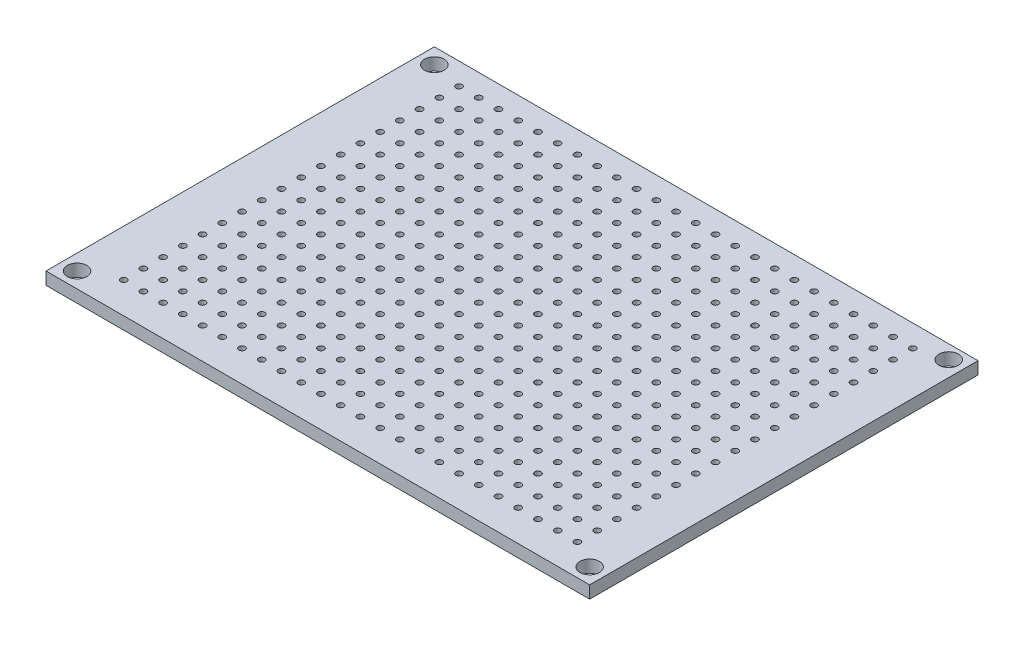
SolidWorks part; units mm, degrees
ref_plane "Front Plane" through (0, 0, 0) normal (0, 0, 1) x (1, 0, 0)
ref_plane "Top Plane" through (0, 0, 0) normal (0, 1, 0) x (1, 0, 0)
ref_plane "Right Plane" through (0, 0, 0) normal (1, 0, 0) x (0, 0, -1)
sketch "Sketch1" plane through (0, 0, 0) normal (0, 1, 0) x (1, 0, 0)
  line L1 (-35, 25) -> (35, 25)
  line L2 (-35, 25) -> (-35, -25)
  line L3 (-35, -25) -> (35, -25)
  line L4 (35, 25) -> (35, -25)
  line L5 (-35, 25) -> (35, -25) construction
  line L6 (-35, -25) -> (35, 25) construction
  point P0 (0, 0)
  dimension "D1" = 70
  dimension "D2" = 50
extrude "Boss-Extrude1" add sketch "Sketch1" along normal blind 1.6
sketch "Sketch2" plane through (0, 1.6, 0) normal (0, 1, 0) x (1, 0, 0)
  line L0 (-35, -25) -> (35, -25) construction
  line L1 (-35, 25) -> (-35, -25) construction
  line L2 (-33, 23) -> (33, 23.2267) construction
  line L3 (33, 23.2267) -> (33, -23) construction
  line L4 (33, -23) -> (-33, -23) construction
  line L5 (-33, -23) -> (-33, 23) construction
  circle A0 centre (-33, 23) radius 1.25
  circle A1 centre (-33, -23) radius 1.25
  circle A2 centre (33, 23.2267) radius 1.25
  circle A3 centre (33, -23) radius 1.25
  circle A4 centre (-29, -21) radius 0.4
  circle A5 centre (-26.46, -21) radius 0.4
  circle A6 centre (-23.92, -21) radius 0.4
  circle A7 centre (-21.38, -21) radius 0.4
  circle A8 centre (-18.84, -21) radius 0.4
  circle A9 centre (-16.3, -21) radius 0.4
  circle A10 centre (-13.76, -21) radius 0.4
  circle A11 centre (-11.22, -21) radius 0.4
  circle A12 centre (-8.68, -21) radius 0.4
  circle A13 centre (-6.14, -21) radius 0.4
  circle A14 centre (-3.6, -21) radius 0.4
  circle A15 centre (-1.06, -21) radius 0.4
  circle A16 centre (1.48, -21) radius 0.4
  circle A17 centre (4.02, -21) radius 0.4
  circle A18 centre (6.56, -21) radius 0.4
  circle A19 centre (9.1, -21) radius 0.4
  circle A20 centre (11.64, -21) radius 0.4
  circle A21 centre (14.18, -21) radius 0.4
  circle A22 centre (16.72, -21) radius 0.4
  circle A23 centre (19.26, -21) radius 0.4
  circle A24 centre (21.8, -21) radius 0.4
  circle A25 centre (24.34, -21) radius 0.4
  circle A26 centre (26.88, -21) radius 0.4
  circle A27 centre (29.42, -21) radius 0.4
  circle A28 centre (-26.46, -18.46) radius 0.4
  circle A29 centre (-23.92, -18.46) radius 0.4
  circle A30 centre (-21.38, -18.46) radius 0.4
  circle A31 centre (-18.84, -18.46) radius 0.4
  circle A32 centre (-16.3, -18.46) radius 0.4
  circle A33 centre (-13.76, -18.46) radius 0.4
  circle A34 centre (-11.22, -18.46) radius 0.4
  circle A35 centre (-8.68, -18.46) radius 0.4
  circle A36 centre (-6.14, -18.46) radius 0.4
  circle A37 centre (-3.6, -18.46) radius 0.4
  circle A38 centre (-1.06, -18.46) radius 0.4
  circle A39 centre (1.48, -18.46) radius 0.4
  circle A40 centre (4.02, -18.46) radius 0.4
  circle A41 centre (6.56, -18.46) radius 0.4
  circle A42 centre (9.1, -18.46) radius 0.4
  circle A43 centre (11.64, -18.46) radius 0.4
  circle A44 centre (14.18, -18.46) radius 0.4
  circle A45 centre (16.72, -18.46) radius 0.4
  circle A46 centre (19.26, -18.46) radius 0.4
  circle A47 centre (21.8, -18.46) radius 0.4
  circle A48 centre (24.34, -18.46) radius 0.4
  circle A49 centre (26.88, -18.46) radius 0.4
  circle A50 centre (29.42, -18.46) radius 0.4
  circle A51 centre (-26.46, -15.92) radius 0.4
  circle A52 centre (-23.92, -15.92) radius 0.4
  circle A53 centre (-21.38, -15.92) radius 0.4
  circle A54 centre (-18.84, -15.92) radius 0.4
  circle A55 centre (-16.3, -15.92) radius 0.4
  circle A56 centre (-13.76, -15.92) radius 0.4
  circle A57 centre (-11.22, -15.92) radius 0.4
  circle A58 centre (-8.68, -15.92) radius 0.4
  circle A59 centre (-6.14, -15.92) radius 0.4
  circle A60 centre (-3.6, -15.92) radius 0.4
  circle A61 centre (-1.06, -15.92) radius 0.4
  circle A62 centre (1.48, -15.92) radius 0.4
  circle A63 centre (4.02, -15.92) radius 0.4
  circle A64 centre (6.56, -15.92) radius 0.4
  circle A65 centre (9.1, -15.92) radius 0.4
  circle A66 centre (11.64, -15.92) radius 0.4
  circle A67 centre (14.18, -15.92) radius 0.4
  circle A68 centre (16.72, -15.92) radius 0.4
  circle A69 centre (19.26, -15.92) radius 0.4
  circle A70 centre (21.8, -15.92) radius 0.4
  circle A71 centre (24.34, -15.92) radius 0.4
  circle A72 centre (26.88, -15.92) radius 0.4
  circle A73 centre (29.42, -15.92) radius 0.4
  circle A74 centre (-26.46, -13.38) radius 0.4
  circle A75 centre (-23.92, -13.38) radius 0.4
  circle A76 centre (-21.38, -13.38) radius 0.4
  circle A77 centre (-18.84, -13.38) radius 0.4
  circle A78 centre (-16.3, -13.38) radius 0.4
  circle A79 centre (-13.76, -13.38) radius 0.4
  circle A80 centre (-11.22, -13.38) radius 0.4
  circle A81 centre (-8.68, -13.38) radius 0.4
  circle A82 centre (-6.14, -13.38) radius 0.4
  circle A83 centre (-3.6, -13.38) radius 0.4
  circle A84 centre (-1.06, -13.38) radius 0.4
  circle A85 centre (1.48, -13.38) radius 0.4
  circle A86 centre (4.02, -13.38) radius 0.4
  circle A87 centre (6.56, -13.38) radius 0.4
  circle A88 centre (9.1, -13.38) radius 0.4
  circle A89 centre (11.64, -13.38) radius 0.4
  circle A90 centre (14.18, -13.38) radius 0.4
  circle A91 centre (16.72, -13.38) radius 0.4
  circle A92 centre (19.26, -13.38) radius 0.4
  circle A93 centre (21.8, -13.38) radius 0.4
  circle A94 centre (24.34, -13.38) radius 0.4
  circle A95 centre (26.88, -13.38) radius 0.4
  circle A96 centre (29.42, -13.38) radius 0.4
  circle A97 centre (-26.46, -10.84) radius 0.4
  circle A98 centre (-23.92, -10.84) radius 0.4
  circle A99 centre (-21.38, -10.84) radius 0.4
  circle A100 centre (-18.84, -10.84) radius 0.4
  circle A101 centre (-16.3, -10.84) radius 0.4
  circle A102 centre (-13.76, -10.84) radius 0.4
  circle A103 centre (-11.22, -10.84) radius 0.4
  circle A104 centre (-8.68, -10.84) radius 0.4
  circle A105 centre (-6.14, -10.84) radius 0.4
  circle A106 centre (-3.6, -10.84) radius 0.4
  circle A107 centre (-1.06, -10.84) radius 0.4
  circle A108 centre (1.48, -10.84) radius 0.4
  circle A109 centre (4.02, -10.84) radius 0.4
  circle A110 centre (6.56, -10.84) radius 0.4
  circle A111 centre (9.1, -10.84) radius 0.4
  circle A112 centre (11.64, -10.84) radius 0.4
  circle A113 centre (14.18, -10.84) radius 0.4
  circle A114 centre (16.72, -10.84) radius 0.4
  circle A115 centre (19.26, -10.84) radius 0.4
  circle A116 centre (21.8, -10.84) radius 0.4
  circle A117 centre (24.34, -10.84) radius 0.4
  circle A118 centre (26.88, -10.84) radius 0.4
  circle A119 centre (29.42, -10.84) radius 0.4
  circle A120 centre (-26.46, -8.3) radius 0.4
  circle A121 centre (-23.92, -8.3) radius 0.4
  circle A122 centre (-21.38, -8.3) radius 0.4
  circle A123 centre (-18.84, -8.3) radius 0.4
  circle A124 centre (-16.3, -8.3) radius 0.4
  circle A125 centre (-13.76, -8.3) radius 0.4
  circle A126 centre (-11.22, -8.3) radius 0.4
  circle A127 centre (-8.68, -8.3) radius 0.4
  circle A128 centre (-6.14, -8.3) radius 0.4
  circle A129 centre (-3.6, -8.3) radius 0.4
  circle A130 centre (-1.06, -8.3) radius 0.4
  circle A131 centre (1.48, -8.3) radius 0.4
  circle A132 centre (4.02, -8.3) radius 0.4
  circle A133 centre (6.56, -8.3) radius 0.4
  circle A134 centre (9.1, -8.3) radius 0.4
  circle A135 centre (11.64, -8.3) radius 0.4
  circle A136 centre (14.18, -8.3) radius 0.4
  circle A137 centre (16.72, -8.3) radius 0.4
  circle A138 centre (19.26, -8.3) radius 0.4
  circle A139 centre (21.8, -8.3) radius 0.4
  circle A140 centre (24.34, -8.3) radius 0.4
  circle A141 centre (26.88, -8.3) radius 0.4
  circle A142 centre (29.42, -8.3) radius 0.4
  circle A143 centre (-26.46, -5.76) radius 0.4
  circle A144 centre (-23.92, -5.76) radius 0.4
  circle A145 centre (-21.38, -5.76) radius 0.4
  circle A146 centre (-18.84, -5.76) radius 0.4
  circle A147 centre (-16.3, -5.76) radius 0.4
  circle A148 centre (-13.76, -5.76) radius 0.4
  circle A149 centre (-11.22, -5.76) radius 0.4
  circle A150 centre (-8.68, -5.76) radius 0.4
  circle A151 centre (-6.14, -5.76) radius 0.4
  circle A152 centre (-3.6, -5.76) radius 0.4
  circle A153 centre (-1.06, -5.76) radius 0.4
  circle A154 centre (1.48, -5.76) radius 0.4
  circle A155 centre (4.02, -5.76) radius 0.4
  circle A156 centre (6.56, -5.76) radius 0.4
  circle A157 centre (9.1, -5.76) radius 0.4
  circle A158 centre (11.64, -5.76) radius 0.4
  circle A159 centre (14.18, -5.76) radius 0.4
  circle A160 centre (16.72, -5.76) radius 0.4
  circle A161 centre (19.26, -5.76) radius 0.4
  circle A162 centre (21.8, -5.76) radius 0.4
  circle A163 centre (24.34, -5.76) radius 0.4
  circle A164 centre (26.88, -5.76) radius 0.4
  circle A165 centre (29.42, -5.76) radius 0.4
  circle A166 centre (-26.46, -3.22) radius 0.4
  circle A167 centre (-23.92, -3.22) radius 0.4
  circle A168 centre (-21.38, -3.22) radius 0.4
  circle A169 centre (-18.84, -3.22) radius 0.4
  circle A170 centre (-16.3, -3.22) radius 0.4
  circle A171 centre (-13.76, -3.22) radius 0.4
  circle A172 centre (-11.22, -3.22) radius 0.4
  circle A173 centre (-8.68, -3.22) radius 0.4
  circle A174 centre (-6.14, -3.22) radius 0.4
  circle A175 centre (-3.6, -3.22) radius 0.4
  circle A176 centre (-1.06, -3.22) radius 0.4
  circle A177 centre (1.48, -3.22) radius 0.4
  circle A178 centre (4.02, -3.22) radius 0.4
  circle A179 centre (6.56, -3.22) radius 0.4
  circle A180 centre (9.1, -3.22) radius 0.4
  circle A181 centre (11.64, -3.22) radius 0.4
  circle A182 centre (14.18, -3.22) radius 0.4
  circle A183 centre (16.72, -3.22) radius 0.4
  circle A184 centre (19.26, -3.22) radius 0.4
  circle A185 centre (21.8, -3.22) radius 0.4
  circle A186 centre (24.34, -3.22) radius 0.4
  circle A187 centre (26.88, -3.22) radius 0.4
  circle A188 centre (29.42, -3.22) radius 0.4
  circle A189 centre (-26.46, -0.68) radius 0.4
  circle A190 centre (-23.92, -0.68) radius 0.4
  circle A191 centre (-21.38, -0.68) radius 0.4
  circle A192 centre (-18.84, -0.68) radius 0.4
  circle A193 centre (-16.3, -0.68) radius 0.4
  circle A194 centre (-13.76, -0.68) radius 0.4
  circle A195 centre (-11.22, -0.68) radius 0.4
  circle A196 centre (-8.68, -0.68) radius 0.4
  circle A197 centre (-6.14, -0.68) radius 0.4
  circle A198 centre (-3.6, -0.68) radius 0.4
  circle A199 centre (-1.06, -0.68) radius 0.4
  circle A200 centre (1.48, -0.68) radius 0.4
  circle A201 centre (4.02, -0.68) radius 0.4
  circle A202 centre (6.56, -0.68) radius 0.4
  circle A203 centre (9.1, -0.68) radius 0.4
  circle A204 centre (11.64, -0.68) radius 0.4
  circle A205 centre (14.18, -0.68) radius 0.4
  circle A206 centre (16.72, -0.68) radius 0.4
  circle A207 centre (19.26, -0.68) radius 0.4
  circle A208 centre (21.8, -0.68) radius 0.4
  circle A209 centre (24.34, -0.68) radius 0.4
  circle A210 centre (26.88, -0.68) radius 0.4
  circle A211 centre (29.42, -0.68) radius 0.4
  circle A212 centre (-26.46, 1.86) radius 0.4
  circle A213 centre (-23.92, 1.86) radius 0.4
  circle A214 centre (-21.38, 1.86) radius 0.4
  circle A215 centre (-18.84, 1.86) radius 0.4
  circle A216 centre (-16.3, 1.86) radius 0.4
  circle A217 centre (-13.76, 1.86) radius 0.4
  circle A218 centre (-11.22, 1.86) radius 0.4
  circle A219 centre (-8.68, 1.86) radius 0.4
  circle A220 centre (-6.14, 1.86) radius 0.4
  circle A221 centre (-3.6, 1.86) radius 0.4
  circle A222 centre (-1.06, 1.86) radius 0.4
  circle A223 centre (1.48, 1.86) radius 0.4
  circle A224 centre (4.02, 1.86) radius 0.4
  circle A225 centre (6.56, 1.86) radius 0.4
  circle A226 centre (9.1, 1.86) radius 0.4
  circle A227 centre (11.64, 1.86) radius 0.4
  circle A228 centre (14.18, 1.86) radius 0.4
  circle A229 centre (16.72, 1.86) radius 0.4
  circle A230 centre (19.26, 1.86) radius 0.4
  circle A231 centre (21.8, 1.86) radius 0.4
  circle A232 centre (24.34, 1.86) radius 0.4
  circle A233 centre (26.88, 1.86) radius 0.4
  circle A234 centre (29.42, 1.86) radius 0.4
  circle A235 centre (-26.46, 4.4) radius 0.4
  circle A236 centre (-23.92, 4.4) radius 0.4
  circle A237 centre (-21.38, 4.4) radius 0.4
  circle A238 centre (-18.84, 4.4) radius 0.4
  circle A239 centre (-16.3, 4.4) radius 0.4
  circle A240 centre (-13.76, 4.4) radius 0.4
  circle A241 centre (-11.22, 4.4) radius 0.4
  circle A242 centre (-8.68, 4.4) radius 0.4
  circle A243 centre (-6.14, 4.4) radius 0.4
  circle A244 centre (-3.6, 4.4) radius 0.4
  circle A245 centre (-1.06, 4.4) radius 0.4
  circle A246 centre (1.48, 4.4) radius 0.4
  circle A247 centre (4.02, 4.4) radius 0.4
  circle A248 centre (6.56, 4.4) radius 0.4
  circle A249 centre (9.1, 4.4) radius 0.4
  circle A250 centre (11.64, 4.4) radius 0.4
  circle A251 centre (14.18, 4.4) radius 0.4
  circle A252 centre (16.72, 4.4) radius 0.4
  circle A253 centre (19.26, 4.4) radius 0.4
  circle A254 centre (21.8, 4.4) radius 0.4
  circle A255 centre (24.34, 4.4) radius 0.4
  circle A256 centre (26.88, 4.4) radius 0.4
  circle A257 centre (29.42, 4.4) radius 0.4
  circle A258 centre (-26.46, 6.94) radius 0.4
  circle A259 centre (-23.92, 6.94) radius 0.4
  circle A260 centre (-21.38, 6.94) radius 0.4
  circle A261 centre (-18.84, 6.94) radius 0.4
  circle A262 centre (-16.3, 6.94) radius 0.4
  circle A263 centre (-13.76, 6.94) radius 0.4
  circle A264 centre (-11.22, 6.94) radius 0.4
  circle A265 centre (-8.68, 6.94) radius 0.4
  circle A266 centre (-6.14, 6.94) radius 0.4
  circle A267 centre (-3.6, 6.94) radius 0.4
  circle A268 centre (-1.06, 6.94) radius 0.4
  circle A269 centre (1.48, 6.94) radius 0.4
  circle A270 centre (4.02, 6.94) radius 0.4
  circle A271 centre (6.56, 6.94) radius 0.4
  circle A272 centre (9.1, 6.94) radius 0.4
  circle A273 centre (11.64, 6.94) radius 0.4
  circle A274 centre (14.18, 6.94) radius 0.4
  circle A275 centre (16.72, 6.94) radius 0.4
  circle A276 centre (19.26, 6.94) radius 0.4
  circle A277 centre (21.8, 6.94) radius 0.4
  circle A278 centre (24.34, 6.94) radius 0.4
  circle A279 centre (26.88, 6.94) radius 0.4
  circle A280 centre (29.42, 6.94) radius 0.4
  circle A281 centre (-26.46, 9.48) radius 0.4
  circle A282 centre (-23.92, 9.48) radius 0.4
  circle A283 centre (-21.38, 9.48) radius 0.4
  circle A284 centre (-18.84, 9.48) radius 0.4
  circle A285 centre (-16.3, 9.48) radius 0.4
  circle A286 centre (-13.76, 9.48) radius 0.4
  circle A287 centre (-11.22, 9.48) radius 0.4
  circle A288 centre (-8.68, 9.48) radius 0.4
  circle A289 centre (-6.14, 9.48) radius 0.4
  circle A290 centre (-3.6, 9.48) radius 0.4
  circle A291 centre (-1.06, 9.48) radius 0.4
  circle A292 centre (1.48, 9.48) radius 0.4
  circle A293 centre (4.02, 9.48) radius 0.4
  circle A294 centre (6.56, 9.48) radius 0.4
  circle A295 centre (9.1, 9.48) radius 0.4
  circle A296 centre (11.64, 9.48) radius 0.4
  circle A297 centre (14.18, 9.48) radius 0.4
  circle A298 centre (16.72, 9.48) radius 0.4
  circle A299 centre (19.26, 9.48) radius 0.4
  circle A300 centre (21.8, 9.48) radius 0.4
  circle A301 centre (24.34, 9.48) radius 0.4
  circle A302 centre (26.88, 9.48) radius 0.4
  circle A303 centre (29.42, 9.48) radius 0.4
  circle A304 centre (-26.46, 12.02) radius 0.4
  circle A305 centre (-23.92, 12.02) radius 0.4
  circle A306 centre (-21.38, 12.02) radius 0.4
  circle A307 centre (-18.84, 12.02) radius 0.4
  circle A308 centre (-16.3, 12.02) radius 0.4
  circle A309 centre (-13.76, 12.02) radius 0.4
  circle A310 centre (-11.22, 12.02) radius 0.4
  circle A311 centre (-8.68, 12.02) radius 0.4
  circle A312 centre (-6.14, 12.02) radius 0.4
  circle A313 centre (-3.6, 12.02) radius 0.4
  circle A314 centre (-1.06, 12.02) radius 0.4
  circle A315 centre (1.48, 12.02) radius 0.4
  circle A316 centre (4.02, 12.02) radius 0.4
  circle A317 centre (6.56, 12.02) radius 0.4
  circle A318 centre (9.1, 12.02) radius 0.4
  circle A319 centre (11.64, 12.02) radius 0.4
  circle A320 centre (14.18, 12.02) radius 0.4
  circle A321 centre (16.72, 12.02) radius 0.4
  circle A322 centre (19.26, 12.02) radius 0.4
  circle A323 centre (21.8, 12.02) radius 0.4
  circle A324 centre (24.34, 12.02) radius 0.4
  circle A325 centre (26.88, 12.02) radius 0.4
  circle A326 centre (29.42, 12.02) radius 0.4
  circle A327 centre (-26.46, 14.56) radius 0.4
  circle A328 centre (-23.92, 14.56) radius 0.4
  circle A329 centre (-21.38, 14.56) radius 0.4
  circle A330 centre (-18.84, 14.56) radius 0.4
  circle A331 centre (-16.3, 14.56) radius 0.4
  circle A332 centre (-13.76, 14.56) radius 0.4
  circle A333 centre (-11.22, 14.56) radius 0.4
  circle A334 centre (-8.68, 14.56) radius 0.4
  circle A335 centre (-6.14, 14.56) radius 0.4
  circle A336 centre (-3.6, 14.56) radius 0.4
  circle A337 centre (-1.06, 14.56) radius 0.4
  circle A338 centre (1.48, 14.56) radius 0.4
  circle A339 centre (4.02, 14.56) radius 0.4
  circle A340 centre (6.56, 14.56) radius 0.4
  circle A341 centre (9.1, 14.56) radius 0.4
  circle A342 centre (11.64, 14.56) radius 0.4
  circle A343 centre (14.18, 14.56) radius 0.4
  circle A344 centre (16.72, 14.56) radius 0.4
  circle A345 centre (19.26, 14.56) radius 0.4
  circle A346 centre (21.8, 14.56) radius 0.4
  circle A347 centre (24.34, 14.56) radius 0.4
  circle A348 centre (26.88, 14.56) radius 0.4
  circle A349 centre (29.42, 14.56) radius 0.4
  circle A350 centre (-26.46, 17.1) radius 0.4
  circle A351 centre (-23.92, 17.1) radius 0.4
  circle A352 centre (-21.38, 17.1) radius 0.4
  circle A353 centre (-18.84, 17.1) radius 0.4
  circle A354 centre (-16.3, 17.1) radius 0.4
  circle A355 centre (-13.76, 17.1) radius 0.4
  circle A356 centre (-11.22, 17.1) radius 0.4
  circle A357 centre (-8.68, 17.1) radius 0.4
  circle A358 centre (-6.14, 17.1) radius 0.4
  circle A359 centre (-3.6, 17.1) radius 0.4
  circle A360 centre (-1.06, 17.1) radius 0.4
  circle A361 centre (1.48, 17.1) radius 0.4
  circle A362 centre (4.02, 17.1) radius 0.4
  circle A363 centre (6.56, 17.1) radius 0.4
  circle A364 centre (9.1, 17.1) radius 0.4
  circle A365 centre (11.64, 17.1) radius 0.4
  circle A366 centre (14.18, 17.1) radius 0.4
  circle A367 centre (16.72, 17.1) radius 0.4
  circle A368 centre (19.26, 17.1) radius 0.4
  circle A369 centre (21.8, 17.1) radius 0.4
  circle A370 centre (24.34, 17.1) radius 0.4
  circle A371 centre (26.88, 17.1) radius 0.4
  circle A372 centre (29.42, 17.1) radius 0.4
  circle A373 centre (-26.46, 19.64) radius 0.4
  circle A374 centre (-23.92, 19.64) radius 0.4
  circle A375 centre (-21.38, 19.64) radius 0.4
  circle A376 centre (-18.84, 19.64) radius 0.4
  circle A377 centre (-16.3, 19.64) radius 0.4
  circle A378 centre (-13.76, 19.64) radius 0.4
  circle A379 centre (-11.22, 19.64) radius 0.4
  circle A380 centre (-8.68, 19.64) radius 0.4
  circle A381 centre (-6.14, 19.64) radius 0.4
  circle A382 centre (-3.6, 19.64) radius 0.4
  circle A383 centre (-1.06, 19.64) radius 0.4
  circle A384 centre (1.48, 19.64) radius 0.4
  circle A385 centre (4.02, 19.64) radius 0.4
  circle A386 centre (6.56, 19.64) radius 0.4
  circle A387 centre (9.1, 19.64) radius 0.4
  circle A388 centre (11.64, 19.64) radius 0.4
  circle A389 centre (14.18, 19.64) radius 0.4
  circle A390 centre (16.72, 19.64) radius 0.4
  circle A391 centre (19.26, 19.64) radius 0.4
  circle A392 centre (21.8, 19.64) radius 0.4
  circle A393 centre (24.34, 19.64) radius 0.4
  circle A394 centre (26.88, 19.64) radius 0.4
  circle A395 centre (29.42, 19.64) radius 0.4
  circle A396 centre (-26.46, 22.18) radius 0.4
  circle A397 centre (-23.92, 22.18) radius 0.4
  circle A398 centre (-21.38, 22.18) radius 0.4
  circle A399 centre (-18.84, 22.18) radius 0.4
  circle A400 centre (-16.3, 22.18) radius 0.4
  circle A401 centre (-13.76, 22.18) radius 0.4
  circle A402 centre (-11.22, 22.18) radius 0.4
  circle A403 centre (-8.68, 22.18) radius 0.4
  circle A404 centre (-6.14, 22.18) radius 0.4
  circle A405 centre (-3.6, 22.18) radius 0.4
  circle A406 centre (-1.06, 22.18) radius 0.4
  circle A407 centre (1.48, 22.18) radius 0.4
  circle A408 centre (4.02, 22.18) radius 0.4
  circle A409 centre (6.56, 22.18) radius 0.4
  circle A410 centre (9.1, 22.18) radius 0.4
  circle A411 centre (11.64, 22.18) radius 0.4
  circle A412 centre (14.18, 22.18) radius 0.4
  circle A413 centre (16.72, 22.18) radius 0.4
  circle A414 centre (19.26, 22.18) radius 0.4
  circle A415 centre (21.8, 22.18) radius 0.4
  circle A416 centre (24.34, 22.18) radius 0.4
  circle A417 centre (26.88, 22.18) radius 0.4
  circle A418 centre (29.42, 22.18) radius 0.4
  circle A419 centre (-29, -18.46) radius 0.4
  circle A420 centre (-29, -15.92) radius 0.4
  circle A421 centre (-29, -13.38) radius 0.4
  circle A422 centre (-29, -10.84) radius 0.4
  circle A423 centre (-29, -8.3) radius 0.4
  circle A424 centre (-29, -5.76) radius 0.4
  circle A425 centre (-29, -3.22) radius 0.4
  circle A426 centre (-29, -0.68) radius 0.4
  circle A427 centre (-29, 1.86) radius 0.4
  circle A428 centre (-29, 4.4) radius 0.4
  circle A429 centre (-29, 6.94) radius 0.4
  circle A430 centre (-29, 9.48) radius 0.4
  circle A431 centre (-29, 12.02) radius 0.4
  circle A432 centre (-29, 14.56) radius 0.4
  circle A433 centre (-29, 17.1) radius 0.4
  circle A434 centre (-29, 19.64) radius 0.4
  circle A435 centre (-29, 22.18) radius 0.4
  dimension "D1" = 46
  dimension "D4" = 2.5
  dimension "D5" = 2.5
  dimension "D6" = 2.5
  dimension "D7" = 2.5
  dimension "D9" = 6
  dimension "D11" = 0.8
  dimension "D2" = 2
  dimension "D3" = 2
  dimension "D8" = 66
  dimension "D10" = 4
  dimension "D12" = 24
  dimension "D13" = 18
extrude "Cut-Extrude1" cut sketch "Sketch2" against normal through all
